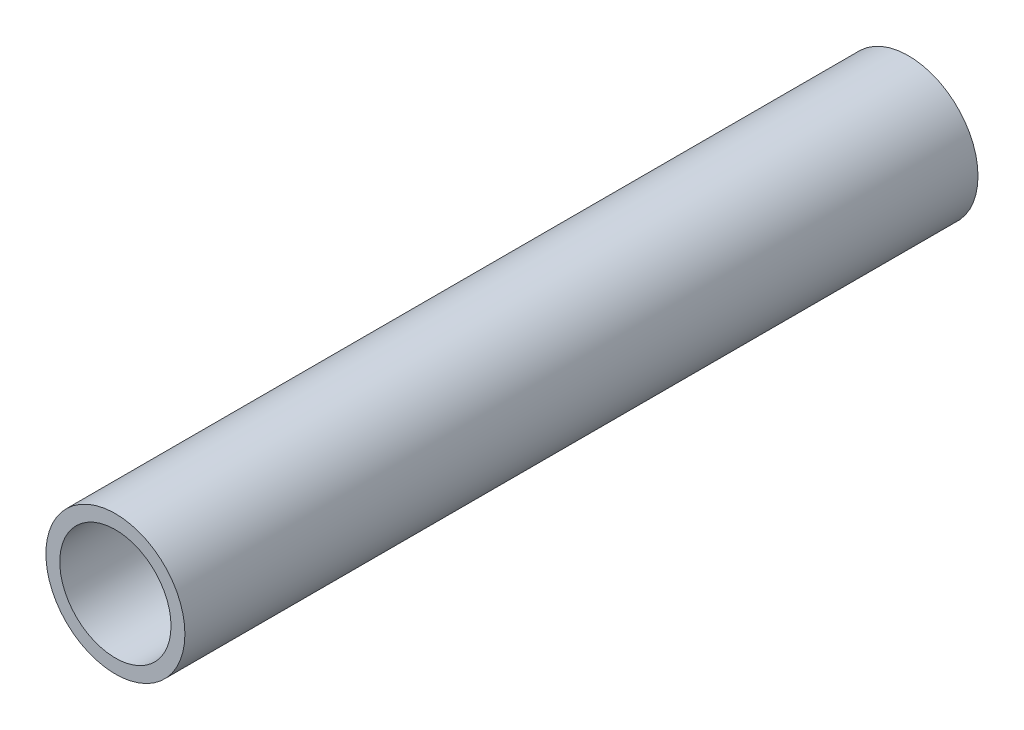
SolidWorks part; units mm, degrees
ref_plane "Front Plane" through (0, 0, 0) normal (0, 0, 1) x (1, 0, 0)
ref_plane "Top Plane" through (0, 0, 0) normal (0, 1, 0) x (1, 0, 0)
ref_plane "Right Plane" through (0, 0, 0) normal (1, 0, 0) x (0, 0, -1)
sketch "Sketch1" plane through (0, 0, 0) normal (0, 0, 1) x (1, 0, 0)
  circle A0 centre (0, 0) radius 1.25
  circle A1 centre (0, 0) radius 1
extrude "Boss-Extrude1" add sketch "Sketch1" along normal blind 14.26
equation "\"D1@Boss-Extrude1\"= \"HL@parametersSketch@prostheticParameters.SLDPRT\" * 0.196 - 4 - 8 - 10'Tube PIP Length"
